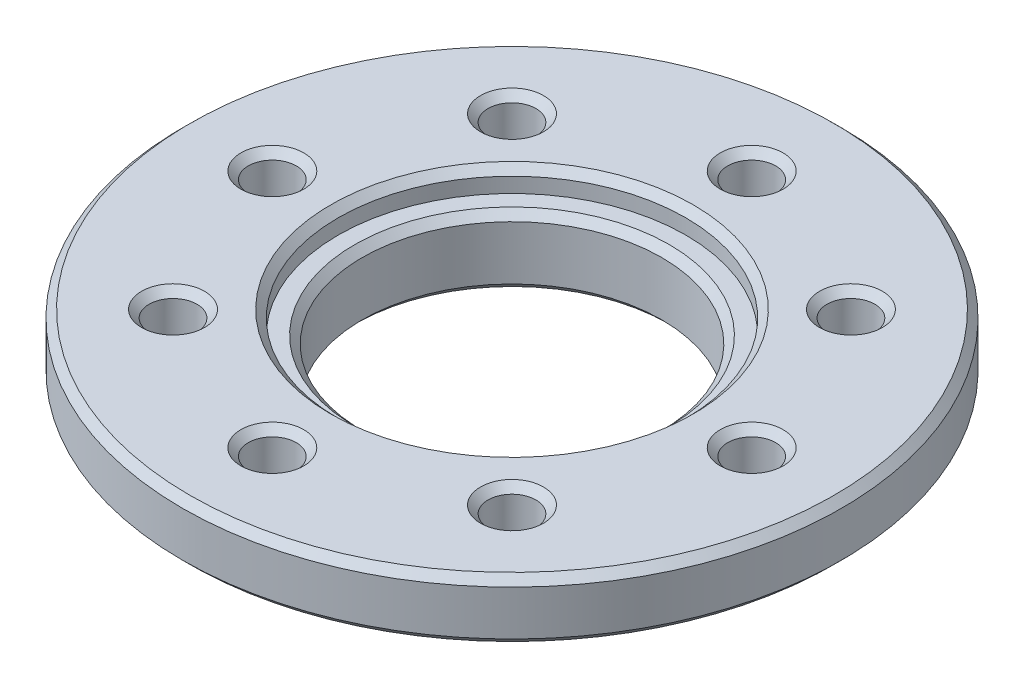
SolidWorks part; units mm, degrees
ref_plane "Front Plane" through (0, 0, 0) normal (0, 0, 1) x (1, 0, 0)
ref_plane "Top Plane" through (0, 0, 0) normal (0, 1, 0) x (1, 0, 0)
ref_plane "Right Plane" through (0, 0, 0) normal (1, 0, 0) x (0, 0, -1)
sketch "Sketch1" plane through (0, 0, 0) normal (0, 0, 1) x (1, 0, 0)
  line L0 (11, 0) -> (0, 0)
  line L1 (0, 0) -> (0, -2)
  line L2 (0, -2) -> (11, -2)
  line L3 (11, -2) -> (11, 0)
  line L4 (0, 0) -> (0, -2) construction
revolve "Revolve1" add sketch "Sketch1" angle 360 about L4
sketch "Sketch2" plane through (0, -2, 0) normal (0, -1, 0) x (1, 0, 0)
  circle A0 centre (0, 0) radius 6.25
extrude "Boss-Extrude1" add sketch "Sketch2" along normal blind 1.05
hole_wizard "Ø1.6 (1.6) Diameter Hole1" positions "Sketch4" profile "Sketch3" hole size "Ø1.6" standard "ANSI Metric"
sketch "Sketch4" plane through (0, 0, 0) normal (0, 1, 0) x (1, 0, 0)
  point P0 (0, 8)
  point P1 (5.6569, 5.6569)
  point P2 (8, 0)
  point P3 (5.6569, -5.6569)
  point P4 (0, -8)
  point P5 (-5.6569, -5.6569)
  point P6 (-8, 0)
  point P7 (-5.6569, 5.6569)
sketch "Sketch3" plane through (0, 0, -8) normal (1, 0, 0) x (0, 0, 1)
  line L0 (0, 0) -> (0, 3.05)
  line L1 (0, 3.05) -> (0.8, 3.05)
  line L2 (0.8, 3.05) -> (0.8, 0)
  line L5 (0.8, 0) -> (0, 0)
  line L11 (0, -6.35) -> (0, 107.95) construction
  dimension "Thru Hole Dia." = 1.6
  dimension "Thru Hole Depth" = 3.05
hole_wizard "CBORE for M8 Hex Head Bolt1" positions "Sketch6" profile "Sketch5" counterbore size "M8" standard "ANSI Metric"
sketch "Sketch6" plane through (0, 0, 0) normal (0, 1, 0) x (1, 0, 0)
  point P0 (0, 0)
sketch "Sketch5" plane through (0, 0, 0) normal (1, 0, 0) x (0, 0, 1)
  line L0 (0, 0) -> (0, 3.05)
  line L1 (0, 3.05) -> (5, 3.05)
  line L3 (5, 3.05) -> (5, 0.75)
  line L4 (5, 0.75) -> (5.8, 0.75)
  line L5 (5.8, 0.75) -> (5.8, 0)
  line L7 (5.8, 0) -> (0, 0)
  line L11 (0, -6.35) -> (0, 107.95) construction
  dimension "Thru Hole Dia." = 10
  dimension "Thru Hole Depth" = 3.05
  dimension "C'Bore Dia." = 11.6
  dimension "C'Bore Depth" = 0.75
chamfer "Chamfer1" distance 0.25 angle 45 14 edges at (8, 0, 0.8) (-8, 0, 0.8) (0, 0, 8.8) (0, -3.05, 5) (0, -2, -11) (0, 0, 5.8) (5.6569, 0, 6.4569) (0, 0, -11) (-5.6569, 0, 6.4569) (0, -3.05, -6.25) (-5.6569, 0, -4.8569) (0, 0, -7.2) (0, -0.75, 5) (5.6569, 0, -4.8569)
